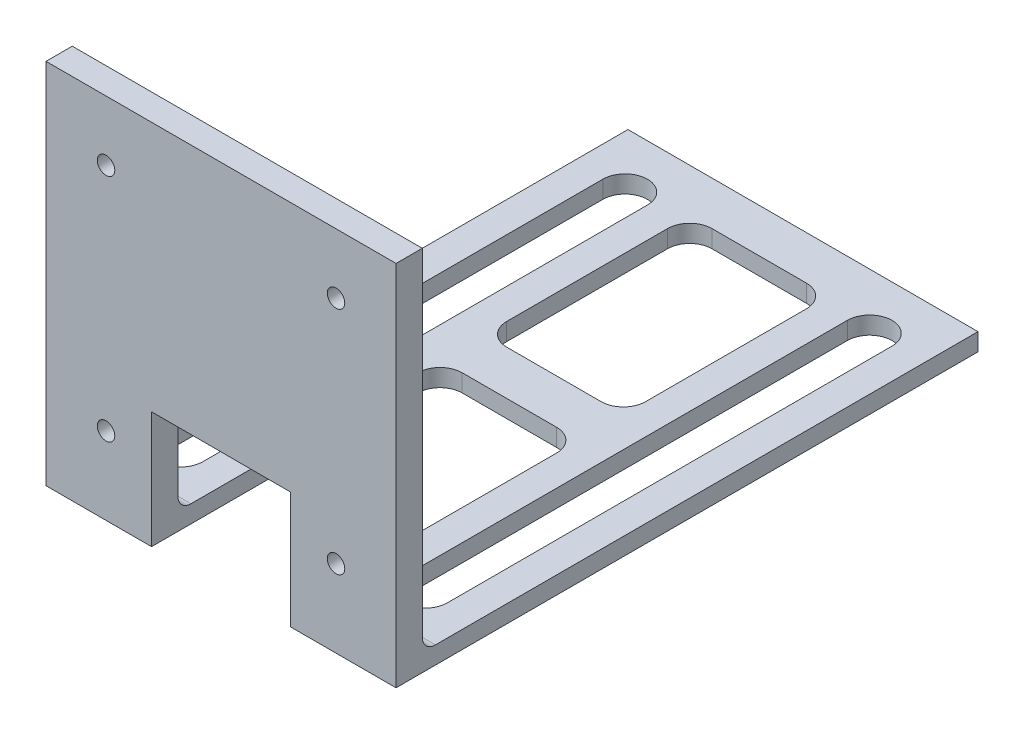
SolidWorks part; units mm, degrees
ref_plane "Front Plane" through (0, 0, 0) normal (0, 0, 1) x (1, 0, 0)
ref_plane "Top Plane" through (0, 0, 0) normal (0, 1, 0) x (1, 0, 0)
ref_plane "Right Plane" through (0, 0, 0) normal (1, 0, 0) x (0, 0, -1)
sketch "Sketch1" plane through (0, 0, 0) normal (0, 0, 1) x (1, 0, 0)
  line L1 (-20, -20) -> (20, -20)
  line L2 (-20, -20) -> (-20, 20)
  line L3 (-20, 20) -> (20, 20)
  line L4 (20, -20) -> (20, 20)
  line L5 (-20, -20) -> (20, 20) construction
  line L6 (-20, 20) -> (20, -20) construction
  line L7 (7.9375, -20) -> (-7.9375, -20)
  line L8 (7.9375, -20) -> (7.9375, -8.65)
  line L9 (7.9375, -8.65) -> (-7.9375, -8.65)
  line L10 (-7.9375, -20) -> (-7.9375, -8.65)
  line L11 (15, -15) -> (-15, -15) construction
  line L12 (15, -15) -> (15, 15) construction
  line L13 (15, 15) -> (-15, 15) construction
  line L14 (-15, -15) -> (-15, 15) construction
  line L15 (15, -15) -> (-15, 15) construction
  line L16 (15, 15) -> (-15, -15) construction
  circle A4 centre (-13.14, -13.14) radius 1
  circle A5 centre (-13.14, 13.14) radius 1
  circle A6 centre (13.14, 13.14) radius 1
  circle A7 centre (13.14, -13.14) radius 1
  point P0 (0, 0)
  point P10 (0, -8.65)
  point P12 (0, 0)
  dimension "D5" = 30
  dimension "D7" = 2
  dimension "D1" = 6.35
  dimension "D2" = 40
  dimension "D3" = 40
  dimension "D4" = 15.875
  dimension "D6" = 30
  dimension "D8" = 1.86
  dimension "D9" = 1.86
  dimension "D10" = 1.86
  dimension "D11" = 1.86
extrude "Boss-Extrude1" add sketch "Sketch1" along normal blind 3 contours L1 L10 L9 L8 L4 L3 L2
sketch "Sketch2" plane through (0, -20, 0) normal (0, -1, 0) x (1, 0, 0)
  line L0 (0, 9.6229) -> (0, -14.2314) construction
  line L1 (-20, 3) -> (-7.9375, 3)
  line L2 (-20, 3) -> (-20, -63.5)
  line L3 (-20, -63.5) -> (-7.9375, -63.5)
  line L4 (-7.9375, 3) -> (-7.9375, -63.5)
  line L5 (-7.9375, 3) -> (-7.9375, 0) construction
  line L6 (-13.9687, -6.35) -> (-13.9687, -57.15) construction
  line L7 (-11.4161, -6.35) -> (-11.4161, -57.15)
  line L8 (-16.5215, -6.35) -> (-16.5214, -57.15)
  line L9 (-20, 0) -> (-7.9375, 0) construction
  line L10 (7.9375, 3) -> (7.9375, -63.5)
  line L11 (20, -63.5) -> (7.9375, -63.5)
  line L12 (20, 3) -> (20, -63.5)
  line L13 (20, 3) -> (7.9375, 3)
  line L14 (13.9688, -6.35) -> (13.9687, -57.15) construction
  line L15 (11.4161, -6.35) -> (11.4161, -57.15)
  line L16 (16.5215, -6.35) -> (16.5214, -57.15)
  arc A0 (-11.4161, -6.35) -> (-16.5215, -6.35) centre (-13.9687, -6.35) ccw
  arc A1 (-16.5214, -57.15) -> (-11.4161, -57.15) centre (-13.9687, -57.15) ccw
  arc A2 (11.4161, -6.35) -> (16.5215, -6.35) centre (13.9688, -6.35) cw
  arc A3 (16.5214, -57.15) -> (11.4161, -57.15) centre (13.9687, -57.15) cw
  point P12 (-13.9687, -31.75)
  point P17 (-13.9688, 3)
  point P26 (13.9688, -31.75)
  dimension "D4" = 5.1054
  dimension "D1" = 50.8
  dimension "D2" = 6.35
  dimension "D3" = 6.35
extrude "Boss-Extrude2" add sketch "Sketch2" along normal blind 2 contours L2 L3 L4 L1
fillet "Fillet1" radius 1.5 2 edges at (-13.9688, -20, 0) (13.9688, -20, 0)
sketch "Sketch3" plane through (0, -20, 0) normal (0, 1, 0) x (1, 0, 0)
  line L0 (7.9375, 1.5) -> (7.9375, 63.5) construction
  line L1 (-7.9375, 63.5) -> (7.9375, 63.5)
  line L2 (-7.9375, 63.5) -> (-7.9375, 58.5)
  line L3 (-7.9375, 58.5) -> (7.9375, 58.5)
  line L4 (7.9375, 63.5) -> (7.9375, 58.5)
  line L5 (-7.9375, 63.5) -> (-7.9375, 1.5) construction
  line L6 (-7.9375, 29.96) -> (7.9375, 29.96)
  line L7 (-7.9375, 29.96) -> (-7.9375, 35.04)
  line L8 (-7.9375, 35.04) -> (7.9375, 35.04)
  line L9 (7.9375, 29.96) -> (7.9375, 35.04)
  point P13 (7.9375, 32.5)
  point P14 (7.9375, 32.5)
  dimension "D1" = 5
  dimension "D2" = 5.08
extrude "Boss-Extrude3" add sketch "Sketch3" against normal up to surface (2 mm away) up to face at (-13.9688, -22, -30.25)
fillet "Fillet2" radius 2.54 6 edges at (7.9375, -21, -58.5) (-7.9375, -21, -58.5) (-7.9375, -21, -29.96) (7.9375, -21, -29.96) (7.9375, -21, -35.04) (-7.9375, -21, -35.04)
